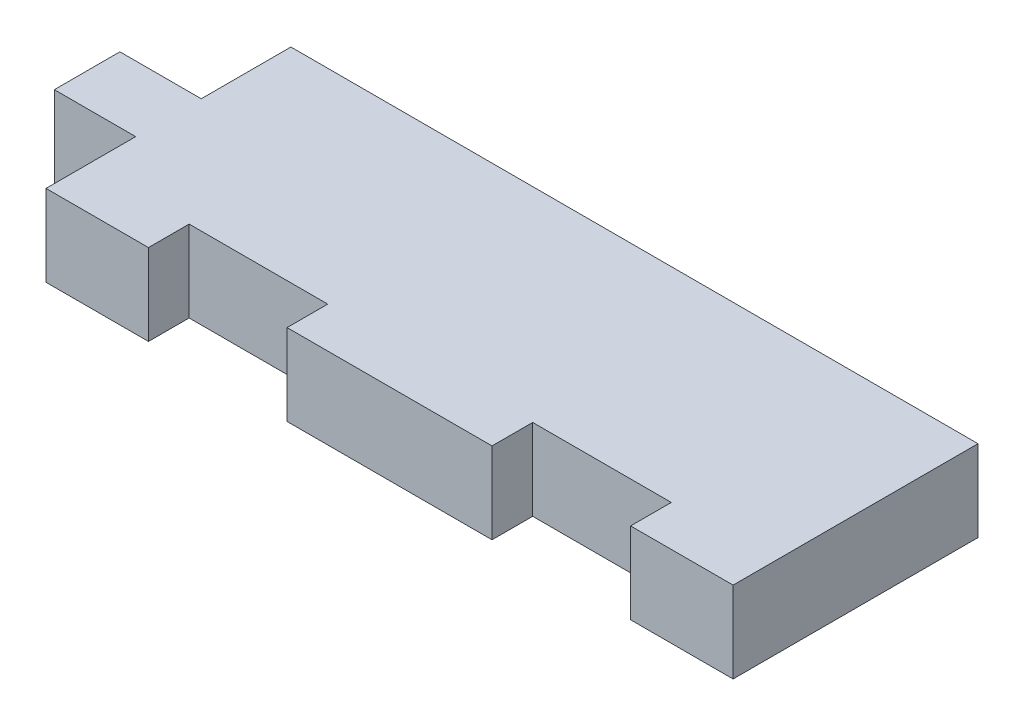
SolidWorks part; units mm, degrees
ref_plane "Front Plane" through (0, 0, 0) normal (0, 0, 1) x (1, 0, 0)
ref_plane "Top Plane" through (0, 0, 0) normal (0, 1, 0) x (1, 0, 0)
ref_plane "Right Plane" through (0, 0, 0) normal (1, 0, 0) x (0, 0, -1)
sketch "Sketch1" plane through (0, 0, 0) normal (0, 1, 0) x (1, 0, 0)
  line L0 (0, 0) -> (0, 9.56) construction
  line L7 (-33.1706, 2.56) -> (-26.8206, 2.56)
  line L9 (-33.1706, -2.56) -> (-26.8206, -2.56)
  line L15 (-33.1706, 2.56) -> (-33.1706, -2.56)
  line L16 (-26.8206, -2.56) -> (-26.8206, -9.56)
  line L17 (-26.8206, 2.56) -> (-26.8206, 9.56)
  line L23 (-26.8206, 9.56) -> (26.8206, 9.56)
  line L24 (-26.8206, -9.56) -> (26.8206, -9.56) construction
  line L25 (26.8206, -9.56) -> (26.8206, 9.56)
  line L26 (0, 0) -> (26.8206, 0) construction
  line L27 (-8, -9.56) -> (8, -9.56)
  line L28 (13.4103, 0) -> (13.4103, -9.56) construction
  line L29 (26.8206, -9.56) -> (18.8206, -9.56)
  line L30 (8, -9.56) -> (8, -6.385)
  line L31 (8, -6.385) -> (18.8206, -6.385)
  line L32 (18.8206, -6.385) -> (18.8206, -9.56)
  line L33 (-18.8206, -6.385) -> (-18.8206, -9.56)
  line L34 (-26.8206, -9.56) -> (-18.8206, -9.56)
  line L35 (-8, -6.385) -> (-18.8206, -6.385)
  line L36 (-8, -6.385) -> (-8, -9.56)
  point P0 (0, 0)
  point P24 (0, -9.56)
  dimension "D1" = 53.6412
  dimension "D2" = 7
  dimension "D3" = 7
  dimension "D4" = 6.35
  dimension "D7" = 3.175
extrude "Boss-Extrude1" add sketch "Sketch1" along normal blind 6.35
